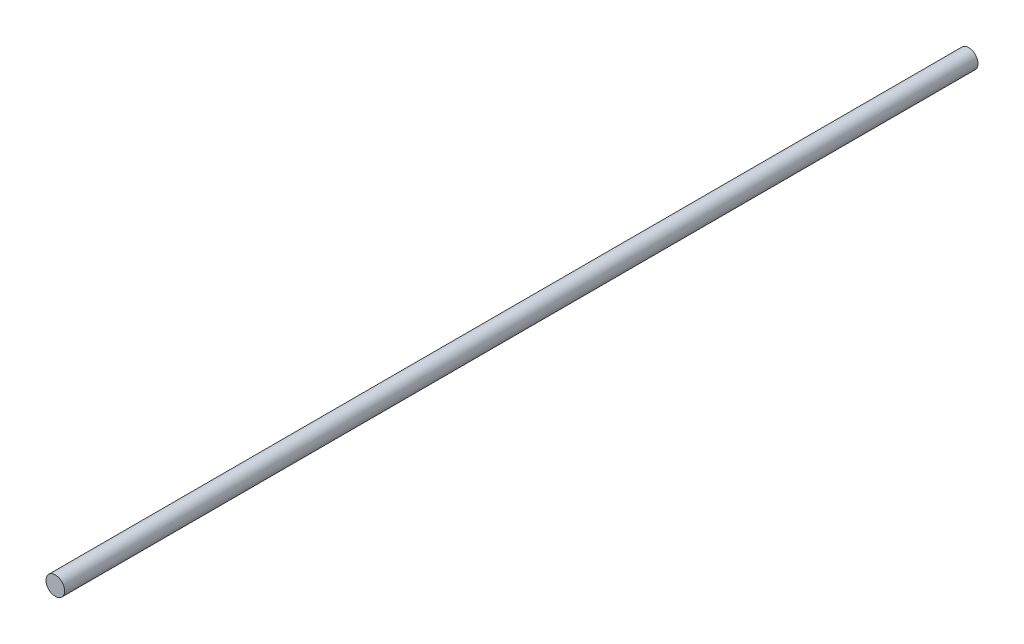
SolidWorks part; units mm, degrees
ref_plane "Front Plane" through (0, 0, 0) normal (0, 0, 1) x (1, 0, 0)
ref_plane "Top Plane" through (0, 0, 0) normal (0, 1, 0) x (1, 0, 0)
ref_plane "Right Plane" through (0, 0, 0) normal (1, 0, 0) x (0, 0, -1)
sketch "Sketch1" plane through (0, 0, 0) normal (0, 0, 1) x (1, 0, 0)
  circle A0 centre (0, 0) radius 10
  dimension "D1" = 20
extrude "Boss-Extrude1" add sketch "Sketch1" along normal blind 980
